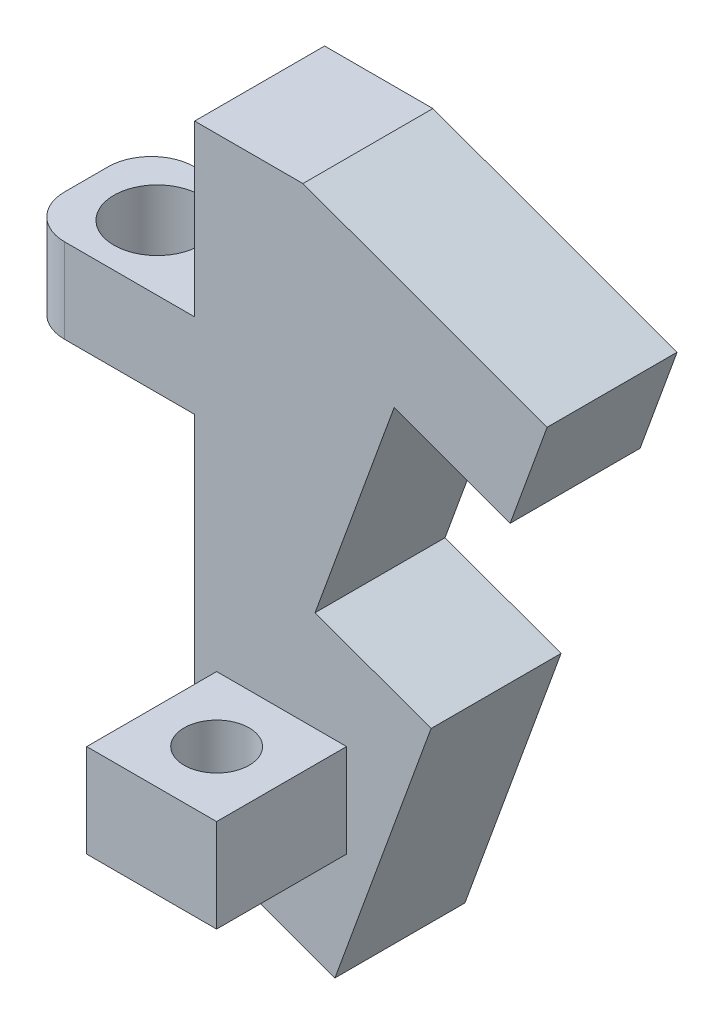
SolidWorks part; units mm, degrees
material "Acrylic (Medium-high impact)"
ref_plane "Front Plane" through (0, 0, 0) normal (0, 0, 1) x (1, 0, 0)
ref_plane "Top Plane" through (0, 0, 0) normal (0, 1, 0) x (1, 0, 0)
ref_plane "Right Plane" through (0, 0, 0) normal (1, 0, 0) x (0, 0, -1)
sketch "Sketch1" plane through (0, 0, 0) normal (0, 0, 1) x (1, 0, 0)
  line L15 (-31.6101, -13.347) -> (-31.6101, -34.177)
  line L30 (-31.6101, -42.0158) -> (-31.6101, -34.177)
  line L37 (-31.6101, -13.347) -> (-26.6101, -13.347)
  line L41 (-26.6101, -13.347) -> (-15.3337, -17.4512)
  line L42 (-17.0438, -22.1497) -> (-22.4001, -20.2001)
  line L47 (-17.0438, -22.1497) -> (-15.3337, -17.4512)
  line L48 (-22.4001, -20.2001) -> (-26.0494, -30.2267)
  line L49 (-26.0494, -30.2267) -> (-20.6932, -32.1762)
  line L50 (-20.6932, -32.1762) -> (-25.1326, -44.3734)
  line L52 (-31.6101, -42.0158) -> (-25.1326, -44.3734)
  line L55 (-20.6859, -32.1465) -> (-25.134, -44.3677) construction
  dimension "D1" = 160
  dimension "D2" = 5
  dimension "D3" = 12
  dimension "D4" = 5
  dimension "D5" = 20.83
  dimension "D6" = 5.7
  dimension "D7" = 10.67
  dimension "D8" = 12.98
extrude "Boss-Extrude1" add sketch "Sketch1" along normal blind 6
sketch "Sketch2" plane through (-31.6101, 0, 0) normal (-1, 0, 0) x (0, 0, 1)
  line L0 (0, -13.347) -> (0, -42.0158) construction
  line L1 (0, -21.1784) -> (6, -21.1784)
  line L2 (0, -21.1784) -> (0, -25.0784)
  line L3 (0, -25.0784) -> (6, -25.0784)
  line L4 (6, -21.1784) -> (6, -25.0784)
  line L5 (6, -13.347) -> (6, -42.0158) construction
  dimension "D1" = 3.9
extrude "Boss-Extrude2" add sketch "Sketch2" along normal blind 8
sketch "Sketch3" plane through (0, -21.1784, 0) normal (0, 1, 0) x (1, 0, 0)
  line L0 (-39.6101, -3) -> (-31.6101, -3) construction
  line L1 (-39.6101, -6) -> (-39.6101, 0) construction
  line L2 (-31.6101, -6) -> (-31.6101, 0) construction
  circle A0 centre (-36.3395, -3) radius 2
  dimension "D1" = 4
extrude "Cut-Extrude2" cut sketch "Sketch3" against normal through all contours A0
fillet "Fillet1" radius 2 2 edges at (-39.6101, -23.1284, 0) (-39.6101, -23.1284, 6)
sketch "Sketch6" plane through (0, 0, 6) normal (0, 0, 1) x (1, 0, 0)
  line L1 (-30.5932, -34.8507) -> (-24.5967, -34.8507)
  line L2 (-30.5932, -34.8507) -> (-30.5932, -39.1507)
  line L3 (-30.5932, -39.1507) -> (-24.5967, -39.1507)
  line L4 (-24.5967, -34.8507) -> (-24.5967, -39.1507)
  dimension "D1" = 5.9965
  dimension "D2" = 4.3
extrude "Boss-Extrude4" add sketch "Sketch6" along normal blind 6
sketch "Sketch7" plane through (0, -39.1507, 0) normal (0, -1, 0) x (1, 0, 0)
  line L0 (-27.5949, 9) -> (-27.5949, 12) construction
  line L1 (-30.5932, 12) -> (-24.5967, 12) construction
  line L2 (-27.5949, 9) -> (-30.5932, 9) construction
  line L3 (-30.5932, 12) -> (-30.5932, 6) construction
  circle A0 centre (-27.5949, 9) radius 1.5
  dimension "D1" = 3
extrude "Cut-Extrude3" cut sketch "Sketch7" against normal through all
